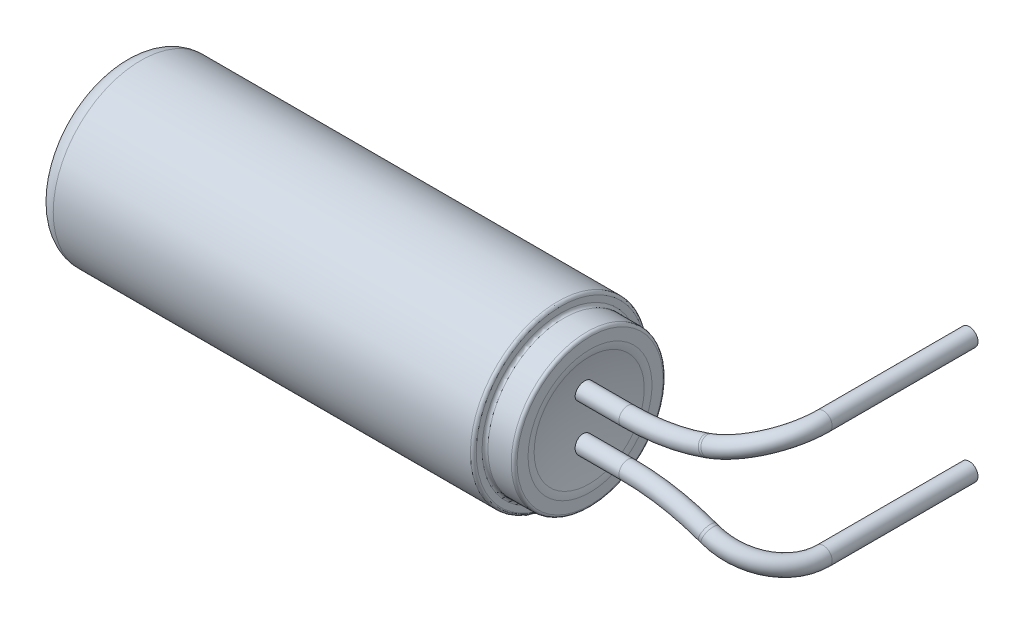
SolidWorks part; units mm, degrees
ref_plane "Спереди" through (0, 0, 0) normal (0, 0, 1) x (1, 0, 0)
ref_plane "Сверху" through (0, 0, 0) normal (0, 1, 0) x (1, 0, 0)
ref_plane "Справа" through (0, 0, 0) normal (1, 0, 0) x (0, 0, -1)
sketch "Эскиз1" plane through (0, 0, 0) normal (0, 1, 0) x (1, 0, 0)
  line L0 (-1006.2679, -1.5) -> (-4.2523, -1.5) construction
  line L1 (-3, -2.5616) -> (-3, -2.75)
  line L2 (-3.55, -3) -> (-10.7, -3)
  line L3 (-11, -2.7) -> (-11, -1.5)
  line L4 (-11, -1.5) -> (-3.127, -1.5)
  line L5 (-3.5, -2.95) -> (-3.5, -2.85)
  line L6 (-3.45, -2.8) -> (-3.05, -2.8)
  arc A1 (-3.127, -1.5) -> (-3.0141, -2.4437) centre (0.873, -1.5) ccw
  arc A2 (-10.7, -3) -> (-11, -2.7) centre (-10.7, -2.7) cw
  arc A3 (-3, -2.75) -> (-3.05, -2.8) centre (-3.05, -2.75) cw
  arc A4 (-3.45, -2.8) -> (-3.5, -2.85) centre (-3.45, -2.85) ccw
  arc A5 (-3.5, -2.95) -> (-3.55, -3) centre (-3.55, -2.95) cw
  arc A6 (-3, -2.5616) -> (-3.0141, -2.4437) centre (-3.5, -2.5616) ccw
  point P1 (0, 0)
  point P16 (-3, -2.8)
  point P19 (-3.5, -2.8)
  point P24 (-3, -2.5)
  dimension "D8" = 4
  dimension "D9" = 0.3
  dimension "D10" = 0.05
  dimension "D11" = 0.5
  dimension "D1" = 1.5
  dimension "D2" = 8
  dimension "D3" = 3
  dimension "D4" = 0.2
  dimension "D5" = 0.5
  dimension "D6" = 3
  dimension "D7" = 0.3
revolve "Повернуть1" add sketch "Эскиз1" angle 360 about L0
sketch3d "Трехмерный эскиз1"
  line L0 (-4, 0.4, 1.5) -> (-2.3538, 0.4, 1.5)
  line L1 (-0.9397, 0.658, 1.5) -> (-0.9857, 0.6412, 1.5)
  line L2 (0, 0, 0) -> (0, 0, 1.5) construction
  line L3 (0, 0, 1.5) -> (0, 0.4, 1.5) construction
  line L4 (0, 0.4, 1.5) -> (-4, 0.4, 1.5) construction
  line L5 (0, 0, 0) -> (0, 1, 0) construction
  line L6 (0, 1, -2) -> (0, 1, 0.5)
  arc A1 (-0.9397, 0.658, 1.5) -> (0, 1, 0.5) centre (-0.9397, 0.658, 0.5) ccw
  arc A2 (-0.9857, 0.6412, 1.5) -> (-2.3538, 0.4, 1.5) centre (-2.3538, 4.4, 1.5) ccw
  point P2 (0, 0, 0)
  point P12 (0, 1, 1.5)
  point P13 (-1.2817, 1.5977, 0.5)
  point P16 (-1.6485, 0.4, 1.5)
  point P17 (-2.3538, 4.4, -2.5)
  dimension "D7" = 1
  dimension "D8" = 4
  dimension "D1" = 1.5
  dimension "D2" = 0.4
  dimension "D3" = 4
  dimension "D4" = 1
  dimension "D5" = 2
  dimension "D6" = 20
ref_plane "Плоскость1" through (-4, 0, 0) normal (1, 0, 0) x (0, 0, -1)
sketch "Эскиз2" plane through (-4, 0, 0) normal (1, 0, 0) x (0, 0, -1)
  circle A0 centre (-1.5, 0.4) radius 0.15
  dimension "D1" = 0.3
sweep "По траектории1" add profiles "Эскиз2" path "Трехмерный эскиз1"
mirror "Зеркальное отражение1" about plane through (0, 0, 0) normal (0, 1, 0) of "По траектории1"
